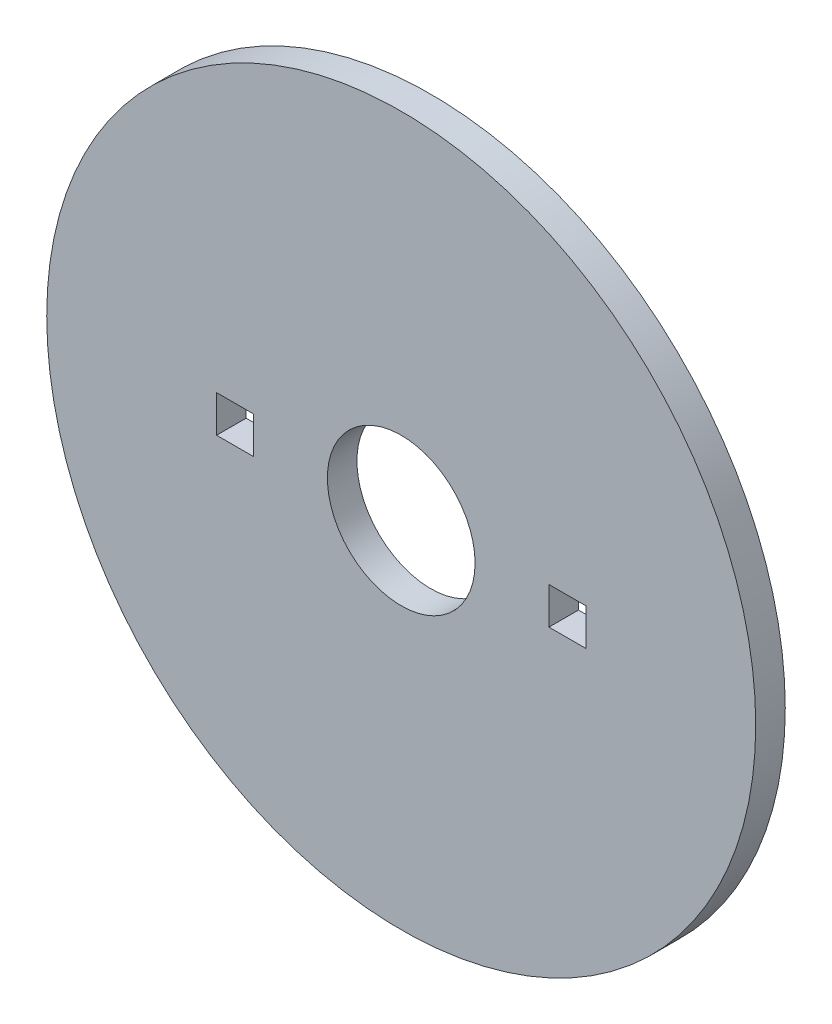
SolidWorks part; units mm, degrees
ref_plane "Front Plane" through (0, 0, 0) normal (0, 0, 1) x (1, 0, 0)
ref_plane "Top Plane" through (0, 0, 0) normal (0, 1, 0) x (1, 0, 0)
ref_plane "Right Plane" through (0, 0, 0) normal (1, 0, 0) x (0, 0, -1)
sketch "Sketch1" plane through (0, 0, 0) normal (0, 0, 1) x (1, 0, 0)
  circle A0 centre (0, 0) radius 9.6
extrude "Boss-Extrude1" add sketch "Sketch1" along normal blind 0.8 contours A0
sketch "Sketch3" plane through (0, 0, 0) normal (0, 0, 1) x (1, 0, 0)
  line L0 (-4, -0.5) -> (-5, -0.5)
  line L1 (4, 0.5) -> (5, 0.5)
  line L2 (4, 0.5) -> (4, -0.5)
  line L3 (4, -0.5) -> (5, -0.5)
  line L4 (5, 0.5) -> (5, -0.5)
  line L5 (-4, -0.5) -> (-4, 0.5)
  line L6 (-4, 0.5) -> (-5, 0.5)
  line L7 (-5, -0.5) -> (-5, 0.5)
  circle A0 centre (0, 0) radius 2
  point P4 (5, 0)
  point P12 (0, 0)
  dimension "D3" = 4
  dimension "D1" = 1
  dimension "D2" = 2
extrude "Cut-Extrude4" cut sketch "Sketch3" against normal through all both and the other way through all from surface at 0.8 starting at face at (9.6, 0, 0.8)
